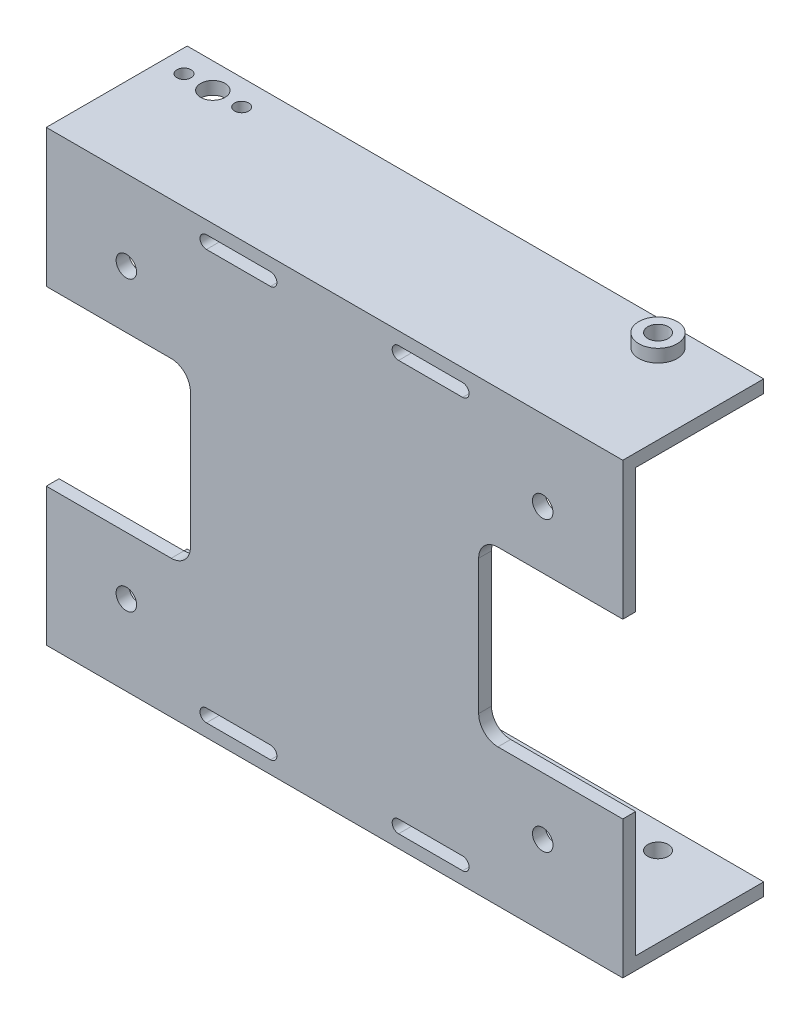
SolidWorks part; units mm, degrees
material "PET"
ref_plane "Спереди" through (0, 0, 0) normal (0, 0, 1) x (1, 0, 0)
ref_plane "Сверху" through (0, 0, 0) normal (0, 1, 0) x (1, 0, 0)
ref_plane "Справа" through (0, 0, 0) normal (1, 0, 0) x (0, 0, -1)
sketch "Эскиз1" plane through (0, 0, 0) normal (0, 0, 1) x (1, 0, 0)
  line L0 (-43, 33) -> (43, -33) construction
  line L1 (-43, -33) -> (43, -33)
  line L2 (-43, -33) -> (-43, 33)
  line L3 (-43, 33) -> (43, 33)
  line L4 (43, -33) -> (43, 33)
  line L8 (-45, -35) -> (45, -35)
  line L9 (45, -35) -> (45, 35)
  line L10 (-45, 35) -> (45, 35)
  line L11 (-45, -35) -> (-45, 35)
  point P0 (0, 0)
  dimension "D1" = 70
  dimension "D2" = 90
  dimension "D3" = 2
extrude "Бобышка-Вытянуть1" add sketch "Эскиз1" along normal blind 22
sketch "Эскиз2" plane through (0, 0, 22) normal (0, 0, 1) x (1, 0, 0)
  line L4 (-45, 35) -> (-45, -35)
  line L5 (-45, -35) -> (45, -35)
  line L6 (45, -35) -> (45, 35)
  line L7 (45, 35) -> (-45, 35)
  line L8 (-45, 35) -> (-45, -35)
  line L9 (-45, -35) -> (45, -35)
  line L10 (45, -35) -> (45, 35)
  line L11 (45, 35) -> (-45, 35)
  dimension "D1" = 0
extrude "Бобышка-Вытянуть2" add sketch "Эскиз2" against normal blind 2
sketch "Эскиз3" plane through (-45, 0, 0) normal (-1, 0, 0) x (0, 0, 1)
  line L0 (0, 35) -> (22, -35) construction
  line L1 (11, 7.5) -> (11, -7.5) construction
  line L2 (17, 7.5) -> (17, -7.5)
  line L3 (5, 7.5) -> (5, -7.5)
  arc A0 (17, 7.5) -> (5, 7.5) centre (11, 7.5) ccw
  arc A1 (5, -7.5) -> (17, -7.5) centre (11, -7.5) ccw
  point P6 (11, 0)
  dimension "D1" = 6
  dimension "D2" = 15
extrude "Вырез-Вытянуть1" cut sketch "Эскиз3" against normal through all both and the other way through all
sketch "Эскиз4" plane through (-45, 0, 0) normal (-1, 0, 0) x (0, 0, 1)
  line L0 (0, 0) -> (22, 0) construction
  line L1 (22, 35) -> (22, -35) construction
  line L2 (11, 26) -> (11, -26) construction
  circle A0 centre (11, 26) radius 1.5
  circle A1 centre (11, -26) radius 1.5
  point P8 (11, 0)
  dimension "D1" = 3
  dimension "D2" = 52
extrude "Вырез-Вытянуть2" cut sketch "Эскиз4" against normal through all both and the other way through all
sketch "Эскиз5" plane through (0, 0, 20) normal (0, 0, -1) x (-1, 0, 0)
  line L0 (-10, 32) -> (-20, 32) construction
  line L1 (15, 32) -> (-15, 32) construction
  line L2 (15, 32) -> (15, -32) construction
  line L3 (15, -32) -> (-15, -32) construction
  line L4 (-15, 32) -> (-15, -32) construction
  line L5 (15, 32) -> (-15, -32) construction
  line L6 (15, -32) -> (-15, 32) construction
  line L7 (-10, 31) -> (-20, 31)
  line L8 (-10, 33) -> (-20, 33)
  line L9 (10, 32) -> (20, 32) construction
  line L10 (10, 33) -> (20, 33)
  line L11 (10, 31) -> (20, 31)
  line L12 (10, -32) -> (20, -32) construction
  line L13 (10, -31) -> (20, -31)
  line L14 (10, -33) -> (20, -33)
  line L15 (-10, -32) -> (-20, -32) construction
  line L16 (-10, -33) -> (-20, -33)
  line L17 (-10, -31) -> (-20, -31)
  line L18 (-43, 33) -> (43, 33) construction
  arc A0 (-10, 31) -> (-10, 33) centre (-10, 32) ccw
  arc A1 (-20, 33) -> (-20, 31) centre (-20, 32) ccw
  arc A2 (10, 33) -> (10, 31) centre (10, 32) ccw
  arc A3 (20, 31) -> (20, 33) centre (20, 32) ccw
  arc A4 (10, -31) -> (10, -33) centre (10, -32) ccw
  arc A5 (20, -33) -> (20, -31) centre (20, -32) ccw
  arc A6 (-10, -33) -> (-10, -31) centre (-10, -32) ccw
  arc A7 (-20, -31) -> (-20, -33) centre (-20, -32) ccw
  point P0 (0, 0)
  point P8 (-15, 32)
  point P14 (15, 32)
  point P21 (15, -32)
  point P28 (-15, -32)
  dimension "D1" = 64
  dimension "D2" = 30
  dimension "D3" = 10
extrude "Вырез-Вытянуть3" cut sketch "Эскиз5" against normal through all both and the other way through all
sketch "Эскиз7" plane through (0, 35, 0) normal (0, 1, 0) x (1, 0, 0)
  line L1 (-37, 0) -> (-37, -4) construction
  line L2 (32.5, 0) -> (32.5, -4) construction
  line L3 (-37, -4) -> (32.5, -4) construction
  line L4 (45, 0) -> (-45, 0) construction
  line L5 (-45, -22) -> (-45, 0) construction
  line L6 (45, -22) -> (45, 0) construction
  circle A0 centre (-37, -4) radius 1.9
  circle A1 centre (32.5, -4) radius 1.6
  dimension "D3" = 3.8
  dimension "D4" = 3.2
  dimension "D1" = 8
  dimension "D2" = 4
  dimension "D5" = 12.5
extrude "Вырез-Вытянуть4" cut sketch "Эскиз7" against normal through all both and the other way through all
sketch "Эскиз9" plane through (0, 35, 0) normal (0, 1, 0) x (1, 0, 0)
  line L0 (-32.5, -4.9) -> (-32.5, -3.1) construction
  line L1 (-41.5, -3.1) -> (-41.5, -4.9) construction
  circle A0 centre (-32.5, -4) radius 1.1
  circle A1 centre (-41.5, -4) radius 1.1
  dimension "D1" = 2.2
extrude "Вырез-Вытянуть5" cut sketch "Эскиз9" against normal through all both and the other way through all
sketch "Эскиз10" plane through (0, 35, 0) normal (0, 1, 0) x (1, 0, 0)
  circle A0 centre (32.5, -4) radius 3
  circle A1 centre (32.5, -4) radius 1.6 construction
  circle A2 centre (32.5, -4) radius 1.6
  dimension "D1" = 6
extrude "Бобышка-Вытянуть3" add sketch "Эскиз10" along normal blind 2
sketch "Эскиз11" plane through (0, -35, 0) normal (0, -1, 0) x (1, 0, 0)
  circle A1 centre (32.5, 4) radius 1.6
  circle A2 centre (32.5, 4) radius 1.6
  circle A3 centre (32.5, 4) radius 3
  circle A4 centre (32.5, 4) radius 3
  dimension "D1" = 0
  dimension "D2" = 0
extrude "Бобышка-Вытянуть4" add sketch "Эскиз11" along normal blind 2
sketch "Эскиз12" plane through (0, 0, 22) normal (0, 0, 1) x (1, 0, 0)
  line L1 (32.5, 22.5) -> (-32.5, 22.5) construction
  line L2 (32.5, 22.5) -> (32.5, -22.5) construction
  line L3 (32.5, -22.5) -> (-32.5, -22.5) construction
  line L4 (-32.5, 22.5) -> (-32.5, -22.5) construction
  line L5 (32.5, 22.5) -> (-32.5, -22.5) construction
  line L6 (32.5, -22.5) -> (-32.5, 22.5) construction
  circle A0 centre (-32.5, 22.5) radius 1.6
  circle A1 centre (-32.5, -22.5) radius 1.6
  circle A2 centre (32.5, -22.5) radius 1.6
  circle A3 centre (32.5, 22.5) radius 1.6
  point P0 (0, 0)
  dimension "D3" = 3.2
  dimension "D1" = 45
  dimension "D2" = 65
extrude "Вырез-Вытянуть6" cut sketch "Эскиз12" against normal through all both and the other way through all
sketch "Эскиз16" plane through (45, 0, 0) normal (1, 0, 0) x (0, 0, -1)
  line L0 (-11, 13.5) -> (-11, -13.5)
  line L1 (-11, -13.5) -> (-22, -13.5)
  line L2 (-22, -35) -> (-22, 35) construction
  line L3 (-22, -13.5) -> (-22, 13.5)
  line L4 (-22, 13.5) -> (-11, 13.5)
  arc A0 (-5, 7.5) -> (-17, 7.5) centre (-11, 7.5) ccw construction
  arc A1 (-17, -7.5) -> (-5, -7.5) centre (-11, -7.5) ccw construction
extrude "Вырез-Вытянуть9" cut sketch "Эскиз16" against normal through all both and the other way through all
sketch "Эскиз17" plane through (0, 0, 22) normal (0, 0, 1) x (1, 0, 0)
  line L0 (-45, -13.5) -> (45, -13.5) construction
  line L1 (22.5, 13.5) -> (-22.5, 13.5)
  line L2 (22.5, 13.5) -> (22.5, -13.5)
  line L3 (22.5, -13.5) -> (-22.5, -13.5)
  line L4 (-22.5, 13.5) -> (-22.5, -13.5)
  line L5 (22.5, 13.5) -> (-22.5, -13.5) construction
  line L6 (22.5, -13.5) -> (-22.5, 13.5) construction
  point P0 (0, 0)
  dimension "D1" = 45
extrude "Бобышка-Вытянуть6" add sketch "Эскиз17" against normal up to surface (2 mm away) up to face at (34.1, -22.5, 20)
fillet "Скругление1" radius 3 4 edges at (-22.5, -13.5, 21) (-22.5, 13.5, 21) (22.5, 13.5, 21) (22.5, -13.5, 21)
sketch "Эскиз18" plane through (43, 0, 0) normal (-1, 0, 0) x (0, 0, 1)
  line L8 (11, 13.5) -> (20, 13.5)
  line L9 (20, 13.5) -> (20, 33)
  line L10 (20, 33) -> (0, 33)
  line L11 (0, 33) -> (0, -33)
  line L12 (0, -33) -> (20, -33)
  line L13 (20, -33) -> (20, -13.5)
  line L14 (20, -13.5) -> (11, -13.5)
  line L15 (5, -7.5) -> (5, 7.5)
  line L16 (11, 13.5) -> (20, 13.5)
  line L17 (20, 13.5) -> (20, 33)
  line L18 (20, 33) -> (0, 33)
  line L19 (0, 33) -> (0, -33)
  line L20 (0, -33) -> (20, -33)
  line L21 (20, -33) -> (20, -13.5)
  line L22 (20, -13.5) -> (11, -13.5)
  line L23 (5, -7.5) -> (5, 7.5)
  arc A2 (5, -7.5) -> (11, -13.5) centre (11, -7.5) ccw
  arc A3 (11, 13.5) -> (5, 7.5) centre (11, 7.5) ccw
  arc A4 (5, -7.5) -> (11, -13.5) centre (11, -7.5) ccw
  arc A5 (11, 13.5) -> (5, 7.5) centre (11, 7.5) ccw
  dimension "D1" = 0
extrude "Вырез-Вытянуть10" cut sketch "Эскиз18" against normal through all both and the other way through all
